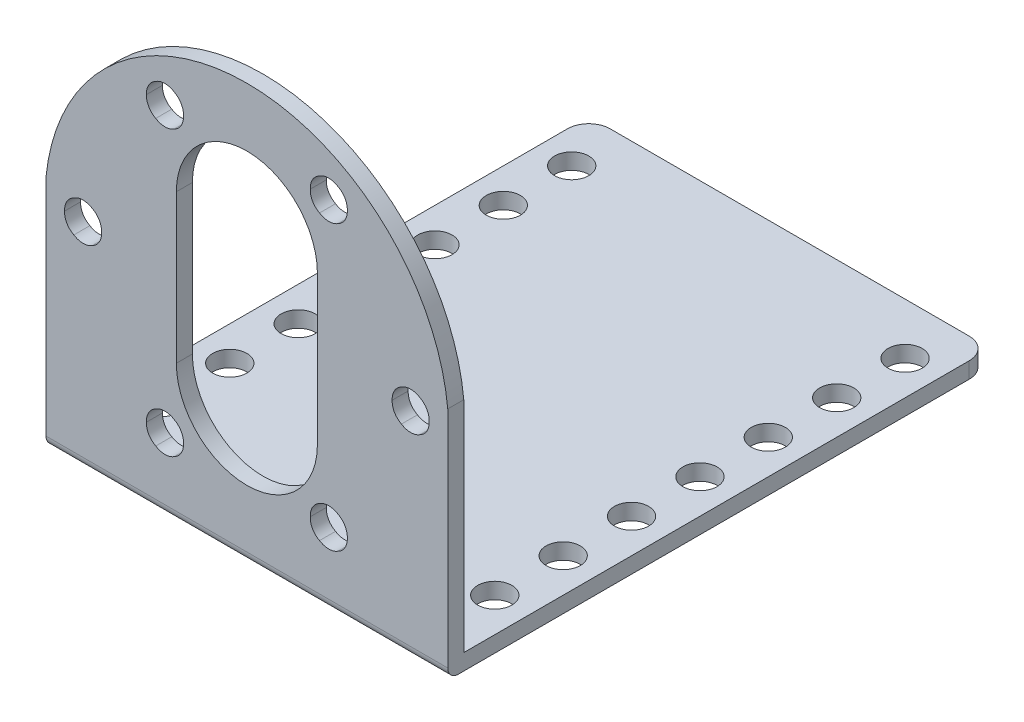
SolidWorks part; units mm, degrees
ref_plane "Front Plane" through (0, 0, 0) normal (0, 0, 1) x (1, 0, 0)
ref_plane "Top Plane" through (0, 0, 0) normal (0, 1, 0) x (1, 0, 0)
ref_plane "Right Plane" through (0, 0, 0) normal (1, 0, 0) x (0, 0, -1)
sketch "Sketch1" plane through (0, 0, 0) normal (0, 0, 1) x (1, 0, 0)
  line L0 (0, 0) -> (0, 39) construction
  line L1 (-18.8, 0) -> (18.8, 0)
  line L2 (-18.8, 0) -> (-18.8, 22)
  line L4 (18.8, 0) -> (18.8, 22)
  line L6 (-6.6, 12.9994) -> (-6.6, 26.8994)
  line L8 (6.6, 12.9994) -> (6.6, 26.8994)
  arc A0 (-18.8, 22) -> (18.8, 22) centre (0, 20.1047) cw
  arc A1 (-6.6, 26.8994) -> (6.6, 26.8994) centre (0, 26.9) cw
  arc A2 (-6.6, 12.9994) -> (6.6, 12.9994) centre (0, 13) ccw
  dimension "D3" = 39
  dimension "D5" = 27.1
  dimension "D6" = 5.5
  dimension "D1" = 37.6
  dimension "D2" = 22
  dimension "D4" = 13.2
  dimension "D7" = 13.9
extrude "Boss-Extrude1" add sketch "Sketch1" along normal blind 1.5
sketch "Sketch2" plane through (0, 0, 0) normal (0, -1, 0) x (1, 0, 0)
  line L0 (18.8, 1.5) -> (18.8, 0) construction
  line L1 (-18.8, 1.5) -> (18.8, 1.5)
  line L2 (-18.8, 1.5) -> (-18.8, -49.3)
  line L3 (-18.8, -49.3) -> (18.8, -49.3)
  line L4 (18.8, 1.5) -> (18.8, -49.3)
  dimension "D1" = 50.8
extrude "Boss-Extrude2" add sketch "Sketch2" against normal blind 1.5
fillet "Fillet1" radius 1 1 edges at (0, 0, 1.5)
fillet "Fillet2" radius 2 2 edges at (-18.8, 0.75, -49.3) (18.8, 0.75, -49.3)
sketch "Sketch3" plane through (0, 0, 0) normal (0, -1, 0) x (1, 0, 0)
  line L0 (-16.8, -49.3) -> (16.8, -49.3) construction
  line L1 (-18.8, 0.5) -> (-18.8, -47.3) construction
  circle A0 centre (-15.6, -44.5) radius 1.6
  dimension "D1" = 3.2
  dimension "D2" = 4.8
  dimension "D3" = 3.2
extrude "Cut-Extrude1" cut sketch "Sketch3" against normal up to next (1.5 mm away)
pattern_linear "LPattern1" count 7 spacing 6.4 along (0, 0, 1) of "Cut-Extrude1"
mirror "Mirror1" about plane through (0, 0, 0) normal (1, 0, 0) of "LPattern1", "Cut-Extrude1"
sketch "Sketch4" plane through (0, 0, 1.5) normal (0, 0, 1) x (1, 0, 0)
  line L0 (0, 0) -> (0, 39) construction
  line L1 (-7.6648, 33.2258) -> (-5.815, 30.0218) construction
  line L2 (-5.815, 30.0218) -> (0, 19.95) construction
  line L3 (0, 19.95) -> (-5.815, 9.8782) construction
  line L4 (0, 19.95) -> (5.815, 9.8782) construction
  line L5 (5.815, 9.8782) -> (7.6648, 6.6742) construction
  line L6 (0, 19.95) -> (5.815, 30.0218) construction
  line L7 (5.815, 30.0218) -> (7.6648, 33.2258) construction
  line L8 (-5.815, 9.8782) -> (-7.6648, 6.6742) construction
  line L9 (7.325, 33.2258) -> (7.6648, 33.2258) construction
  line L10 (7.6648, 33.2258) -> (9.5146, 36.4297) construction
  circle A0 centre (7.6648, 33.2258) radius 1.6
  arc A1 (18.8, 22) -> (-18.8, 22) centre (0, 20.1047) ccw construction
  circle A3 centre (15.3295, 19.95) radius 1.6
  circle A4 centre (7.6648, 6.6742) radius 1.6
  circle A5 centre (-7.6648, 6.6742) radius 1.6
  circle A6 centre (-15.3295, 19.95) radius 1.6
  circle A7 centre (-7.6648, 33.2258) radius 1.6
  arc A8 (-6.6, 12.9994) -> (6.6, 12.9994) centre (0, 13) ccw construction
  arc A9 (6.6, 26.8994) -> (-6.6, 26.8994) centre (0, 26.9) ccw construction
  point P26 (0, 19.95)
  dimension "D1" = 3.2
  dimension "D2" = 6
extrude "Cut-Extrude2" cut sketch "Sketch4" against normal up to next (1.5 mm away)
pattern_circular "CirPattern1" count 6 over 360 about axis through (0, 20.1047, 0) along (0, 0, 1) of "Cut-Extrude2"
sketch "Sketch5" plane through (0, 0, 0) normal (0, -1, 0) x (1, 0, 0)
  line L0 (18.8, 0.5) -> (-18.8, 0.5) construction
  line L1 (18.8, 0.5) -> (18.8, -47.3) construction
  line L2 (-16.8, -49.3) -> (16.8, -49.3) construction
  line L3 (-18.8, 0.5) -> (-18.8, -47.3) construction
  line L4 (18.8, 0.5) -> (-18.8, 0.5)
  line L5 (18.8, 0.5) -> (18.8, -47.3)
  line L6 (-16.8, -49.3) -> (16.8, -49.3)
  line L7 (-18.8, 0.5) -> (-18.8, -47.3)
  circle A0 centre (15.6, -12.5) radius 1.6 construction
  circle A1 centre (15.6, -12.5) radius 1.6
  circle A3 centre (15.6, -6.1) radius 1.6
  circle A4 centre (15.6, -6.1) radius 1.6
  circle A5 centre (15.6, -18.9) radius 1.6
  circle A6 centre (15.6, -18.9) radius 1.6
  circle A7 centre (15.6, -25.3) radius 1.6
  circle A8 centre (15.6, -25.3) radius 1.6
  circle A9 centre (15.6, -31.7) radius 1.6
  circle A10 centre (15.6, -31.7) radius 1.6
  circle A11 centre (15.6, -38.1) radius 1.6
  circle A12 centre (15.6, -38.1) radius 1.6
  circle A13 centre (15.6, -44.5) radius 1.6
  circle A14 centre (15.6, -44.5) radius 1.6
  circle A15 centre (-15.6, -44.5) radius 1.6
  circle A16 centre (-15.6, -44.5) radius 1.6
  circle A17 centre (-15.6, -38.1) radius 1.6
  circle A18 centre (-15.6, -38.1) radius 1.6
  circle A19 centre (-15.6, -31.7) radius 1.6
  circle A20 centre (-15.6, -31.7) radius 1.6
  circle A21 centre (-15.6, -25.3) radius 1.6
  circle A22 centre (-15.6, -25.3) radius 1.6
  circle A23 centre (-15.6, -18.9) radius 1.6
  circle A24 centre (-15.6, -18.9) radius 1.6
  circle A25 centre (-15.6, -12.5) radius 1.6
  circle A26 centre (-15.6, -12.5) radius 1.6
  circle A27 centre (-15.6, -6.1) radius 1.6
  circle A28 centre (-15.6, -6.1) radius 1.6
  dimension "D1" = 0
  dimension "D2" = 0
  dimension "D3" = 0
  dimension "D4" = 0
  dimension "D5" = 0
  dimension "D6" = 0
  dimension "D7" = 0
  dimension "D8" = 0
  dimension "D9" = 0
  dimension "D10" = 0
  dimension "D11" = 0
  dimension "D12" = 0
  dimension "D13" = 0
